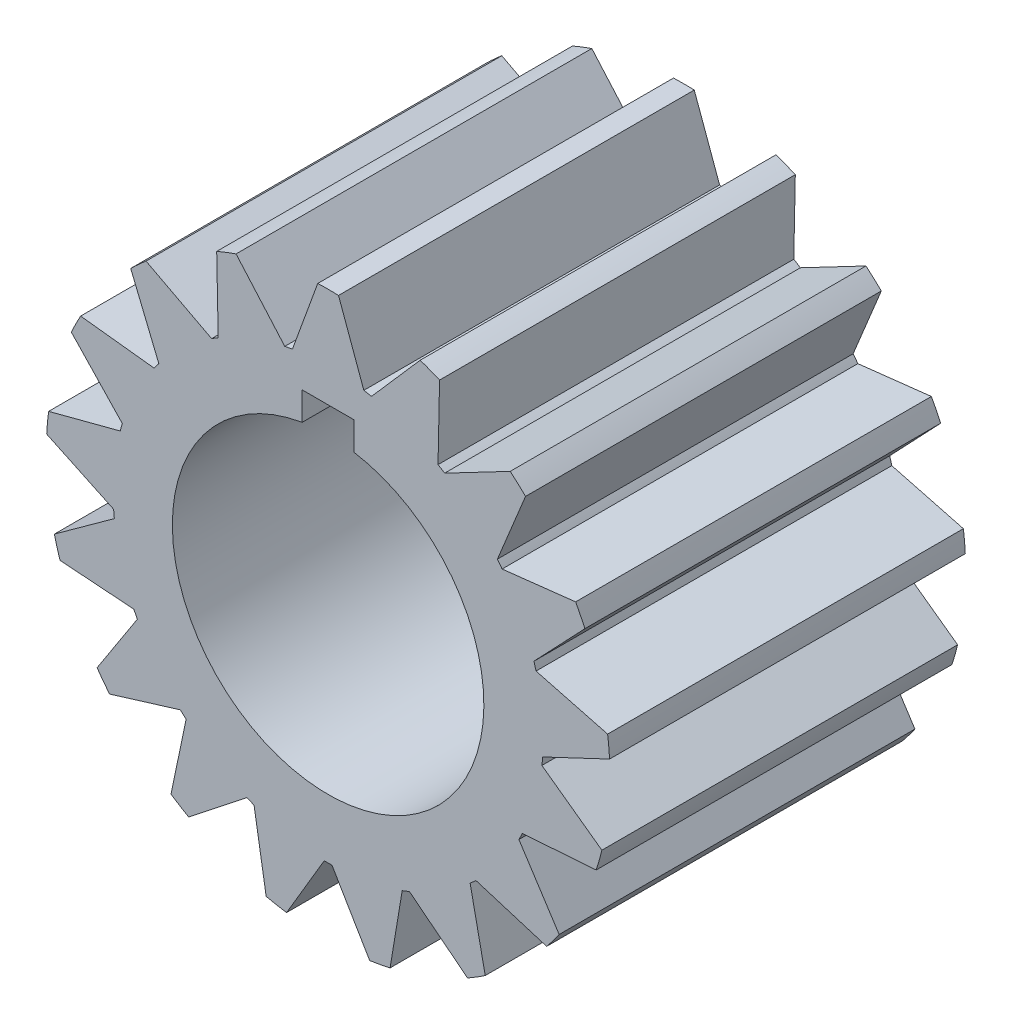
SolidWorks part; units mm, degrees
ref_plane "Front Plane" through (0, 0, 0) normal (0, 0, 1) x (1, 0, 0)
ref_plane "Top Plane" through (0, 0, 0) normal (0, 1, 0) x (1, 0, 0)
ref_plane "Right Plane" through (0, 0, 0) normal (1, 0, 0) x (0, 0, -1)
sketch "Sketch2" plane through (0, 0, 0) normal (0, 0, 1) x (1, 0, 0)
  line L0 (-4.366, 25.9419) -> (-1.27, 34.4482)
  line L1 (1.27, 34.4482) -> (4.366, 25.9419)
  line L2 (0, 0) -> (0, 34.4716) construction
  line L3 (5.3001, 25.7673) -> (11.2599, 32.5808)
  line L4 (13.6284, 31.6632) -> (13.4425, 22.613)
  line L5 (14.2504, 22.1127) -> (22.2691, 26.3131)
  line L6 (24.1461, 24.6019) -> (20.7035, 16.23)
  line L7 (21.2762, 15.4716) -> (30.2707, 16.4917)
  line L8 (31.4029, 14.218) -> (25.1684, 7.655)
  line L9 (25.4284, 6.741) -> (34.1841, 4.4431)
  line L10 (34.4184, 1.9139) -> (26.2341, -1.9538)
  line L11 (26.1464, -2.9) -> (33.4807, -8.2057)
  line L12 (32.7856, -10.6487) -> (23.7568, -11.2987)
  line L13 (23.3332, -12.1493) -> (28.2556, -19.7462)
  line L14 (26.7249, -21.7732) -> (18.071, -19.1177)
  line L15 (17.3687, -19.7579) -> (19.2144, -28.6199)
  line L16 (17.0549, -29.957) -> (9.9446, -24.3547)
  line L17 (9.0585, -24.698) -> (7.5782, -33.6283)
  line L18 (5.0815, -34.095) -> (0.4751, -26.3025)
  line L19 (-0.4751, -26.3025) -> (-5.0815, -34.095)
  line L20 (-7.5782, -33.6283) -> (-9.0585, -24.698)
  line L21 (-9.9446, -24.3547) -> (-17.0549, -29.957)
  line L22 (-19.2144, -28.6199) -> (-17.3687, -19.7579)
  line L23 (-18.071, -19.1177) -> (-26.7249, -21.7732)
  line L24 (-28.2556, -19.7462) -> (-23.3332, -12.1493)
  line L25 (-23.7568, -11.2987) -> (-32.7856, -10.6487)
  line L26 (-33.4807, -8.2057) -> (-26.1464, -2.9)
  line L27 (-26.2341, -1.9538) -> (-34.4184, 1.9139)
  line L28 (-34.1841, 4.4431) -> (-25.4284, 6.741)
  line L29 (-25.1684, 7.655) -> (-31.4029, 14.218)
  line L30 (-30.2707, 16.4917) -> (-21.2762, 15.4716)
  line L31 (-20.7035, 16.23) -> (-24.1461, 24.6019)
  line L32 (-22.2691, 26.3131) -> (-14.2504, 22.1127)
  line L33 (-13.4425, 22.613) -> (-13.6284, 31.6632)
  line L34 (-11.2599, 32.5808) -> (-5.3001, 25.7673)
  arc A0 (-4.366, 25.9419) -> (-5.3001, 25.7673) centre (0, 0) ccw
  arc A1 (1.27, 34.4482) -> (-1.27, 34.4482) centre (0, 0) ccw
  arc A2 (13.6284, 31.6632) -> (11.2599, 32.5808) centre (0, 0) ccw
  arc A3 (24.1461, 24.6019) -> (22.2691, 26.3131) centre (0, 0) ccw
  arc A4 (31.4029, 14.218) -> (30.2707, 16.4917) centre (0, 0) ccw
  arc A5 (34.4184, 1.9139) -> (34.1841, 4.4431) centre (0, 0) ccw
  arc A6 (32.7856, -10.6487) -> (33.4807, -8.2057) centre (0, 0) ccw
  arc A7 (26.7249, -21.7732) -> (28.2556, -19.7462) centre (0, 0) ccw
  arc A8 (17.0549, -29.957) -> (19.2144, -28.6199) centre (0, 0) ccw
  arc A9 (5.0815, -34.095) -> (7.5782, -33.6283) centre (0, 0) ccw
  arc A10 (-7.5782, -33.6283) -> (-5.0815, -34.095) centre (0, 0) ccw
  arc A11 (-19.2144, -28.6199) -> (-17.0549, -29.957) centre (0, 0) ccw
  arc A12 (-28.2556, -19.7462) -> (-26.7249, -21.7732) centre (0, 0) ccw
  arc A13 (-33.4807, -8.2057) -> (-32.7856, -10.6487) centre (0, 0) ccw
  arc A14 (-34.1841, 4.4431) -> (-34.4184, 1.9139) centre (0, 0) ccw
  arc A15 (-30.2707, 16.4917) -> (-31.4029, 14.218) centre (0, 0) ccw
  arc A16 (-22.2691, 26.3131) -> (-24.1461, 24.6019) centre (0, 0) ccw
  arc A17 (-11.2599, 32.5808) -> (-13.6284, 31.6632) centre (0, 0) ccw
  arc A18 (-13.4425, 22.613) -> (-14.2504, 22.1127) centre (0, 0) ccw
  arc A19 (-20.7035, 16.23) -> (-21.2762, 15.4716) centre (0, 0) ccw
  arc A20 (-25.1684, 7.655) -> (-25.4284, 6.741) centre (0, 0) ccw
  arc A21 (-26.2341, -1.9538) -> (-26.1464, -2.9) centre (0, 0) ccw
  arc A22 (-23.7568, -11.2987) -> (-23.3332, -12.1493) centre (0, 0) ccw
  arc A23 (-18.071, -19.1177) -> (-17.3687, -19.7579) centre (0, 0) ccw
  arc A24 (-9.9446, -24.3547) -> (-9.0585, -24.698) centre (0, 0) ccw
  arc A25 (-0.4751, -26.3025) -> (0.4751, -26.3025) centre (0, 0) ccw
  arc A26 (9.0585, -24.698) -> (9.9446, -24.3547) centre (0, 0) ccw
  arc A27 (17.3687, -19.7579) -> (18.071, -19.1177) centre (0, 0) ccw
  arc A28 (23.3332, -12.1493) -> (23.7568, -11.2987) centre (0, 0) ccw
  arc A29 (26.1464, -2.9) -> (26.2341, -1.9538) centre (0, 0) ccw
  arc A30 (25.4284, 6.741) -> (25.1684, 7.655) centre (0, 0) ccw
  arc A31 (21.2762, 15.4716) -> (20.7035, 16.23) centre (0, 0) ccw
  arc A32 (14.2504, 22.1127) -> (13.4425, 22.613) centre (0, 0) ccw
  arc A33 (5.3001, 25.7673) -> (4.366, 25.9419) centre (0, 0) ccw
  point P75 (0, 0)
  dimension "D1" = 52.6136
  dimension "D2" = 68.9432
  dimension "D3" = 1.27
  dimension "D4" = 1.27
  dimension "D5" = 20
  dimension "D6" = 20
  dimension "D7" = 17
extrude "Boss-Extrude1" add sketch "Sketch2" along normal blind 43.5102
sketch "Sketch4" plane through (0, 0, 43.5102) normal (0, 0, 1) x (1, 0, 0)
  line L0 (0, 0) -> (0, 29.3306) construction
  line L1 (-3.175, 22.225) -> (3.175, 22.225)
  line L2 (-3.175, 22.225) -> (-3.175, 18.7836)
  line L4 (3.175, 22.225) -> (3.175, 18.7836)
  line L5 (3.175, 19.05) -> (5.6842, 19.05) construction
  arc A0 (-3.175, 18.7836) -> (3.175, 18.7836) centre (0, 0) ccw
  point P7 (0, 22.225)
  dimension "D1" = 38.1
  dimension "D2" = 3.175
  dimension "D3" = 6.35
extrude "Cut-Extrude1" cut sketch "Sketch4" against normal up to surface (43.5102 mm away) up to face at (0, 0, 0)
